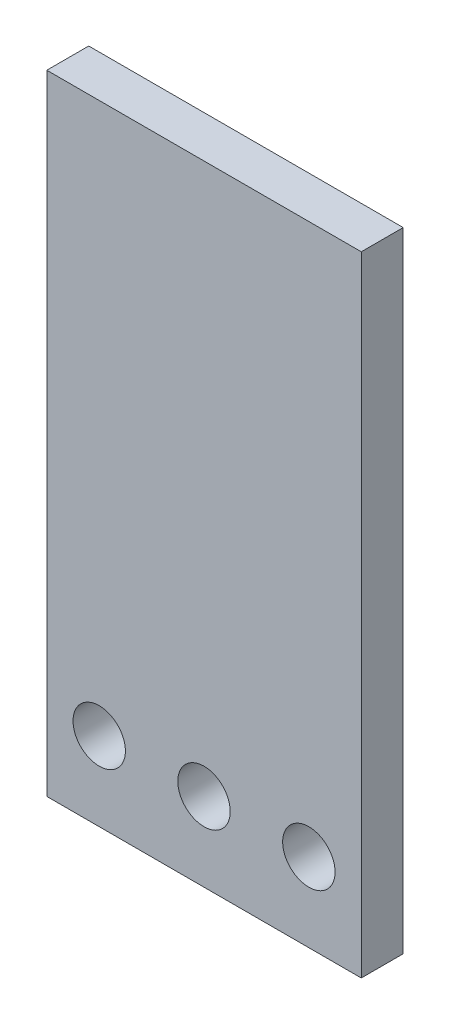
SolidWorks part; units mm, degrees
material "Hexcel AS4C (3000 Filaments)"
ref_plane "Front Plane" through (0, 0, 0) normal (0, 0, 1) x (1, 0, 0)
ref_plane "Top Plane" through (0, 0, 0) normal (0, 1, 0) x (1, 0, 0)
ref_plane "Right Plane" through (0, 0, 0) normal (1, 0, 0) x (0, 0, -1)
sketch "Sketch1" plane through (0, 0, 0) normal (0, 0, 1) x (1, 0, 0)
  line L0 (0, 19.05) -> (76.2, 19.05) construction
  line L1 (0, 0) -> (76.2, 0)
  line L2 (0, 0) -> (0, 152.4)
  line L3 (0, 152.4) -> (76.2, 152.4)
  line L4 (76.2, 0) -> (76.2, 152.4)
  circle A0 centre (12.7, 19.05) radius 6.35
  circle A1 centre (38.1, 19.05) radius 6.35
  circle A2 centre (63.5, 19.05) radius 6.35
  point P13 (0, 0)
  point P14 (0, 0)
  point P15 (0, 0)
  point P16 (33.0364, 19.05)
  point P17 (38.1, 19.05)
  dimension "D3" = 12.7
  dimension "D1" = 152.4
  dimension "D2" = 76.2
  dimension "D4" = 19.05
  dimension "D5" = 25.4
  dimension "D6" = 25.4
extrude "Boss-Extrude1" add sketch "Sketch1" along normal blind 10.16
